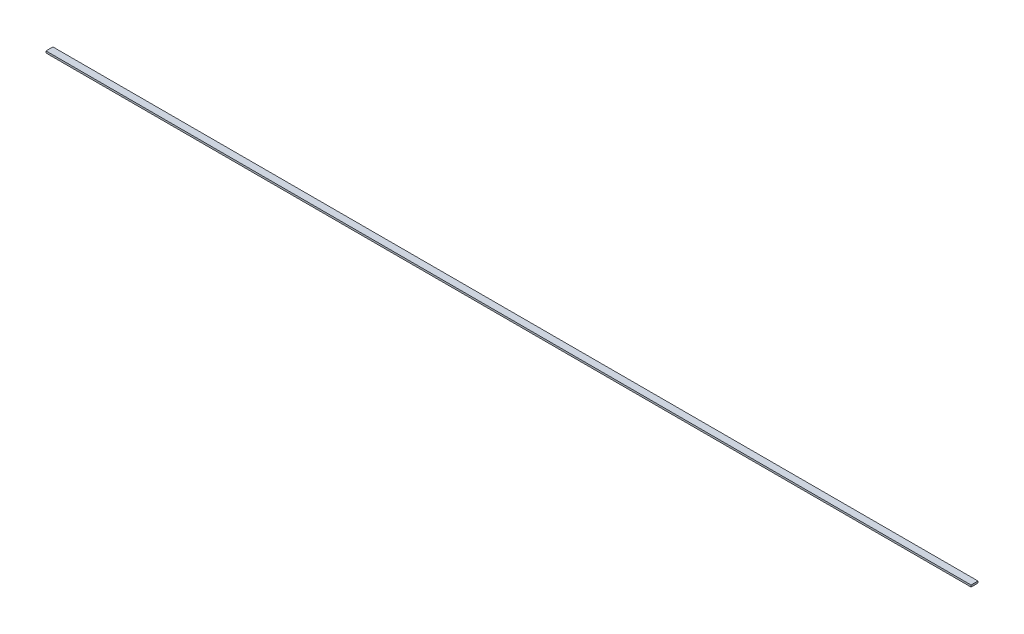
SolidWorks part; units mm, degrees
ref_plane "Спереди" through (0, 0, 0) normal (0, 0, 1) x (1, 0, 0)
ref_plane "Сверху" through (0, 0, 0) normal (0, 1, 0) x (1, 0, 0)
ref_plane "Справа" through (0, 0, 0) normal (1, 0, 0) x (0, 0, -1)
ref_plane "Плоскость4" through (0, -0.545, 0) normal (0, -1, 0) x (1, 0, 0)
sketch "Эскиз1" plane through (0, -0.545, 0) normal (0, -1, 0) x (1, 0, 0)
  line L0 (-275, 0) -> (275, 0)
  line L1 (275, 0) -> (275, 4.125)
  line L2 (275, 4.125) -> (-275, 4.125)
  line L3 (-275, 4.125) -> (-275, 0)
  dimension "D1" = 550
extrude "Бобышка-Вытянуть1" add sketch "Эскиз1" against normal blind 1.09
